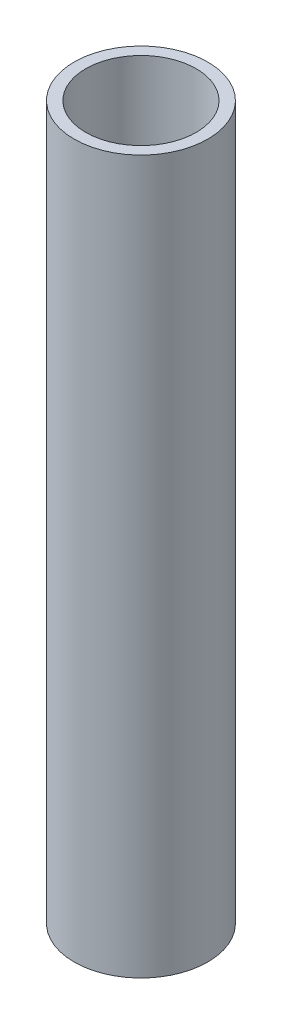
SolidWorks part; units mm, degrees
material "6061 Alloy"
ref_plane "Front Plane" through (0, 0, 0) normal (0, 0, 1) x (1, 0, 0)
ref_plane "Top Plane" through (0, 0, 0) normal (0, 1, 0) x (1, 0, 0)
ref_plane "Right Plane" through (0, 0, 0) normal (1, 0, 0) x (0, 0, -1)
sketch "Sketch1" plane through (0, 0, 0) normal (0, 1, 0) x (1, 0, 0)
  circle A0 centre (0, 0) radius 7.874
  circle A1 centre (0, 0) radius 9.525
  dimension "D1" = 19.05
  dimension "D2" = 1.651
sketch "Sketch2" plane through (0, 0, 0) normal (0, 0, 1) x (1, 0, 0)
  line L0 (0, 0) -> (0, 101.6)
  dimension "D1" = 101.6
sweep "Sweep1" add profiles "Sketch1" path "Sketch2"
